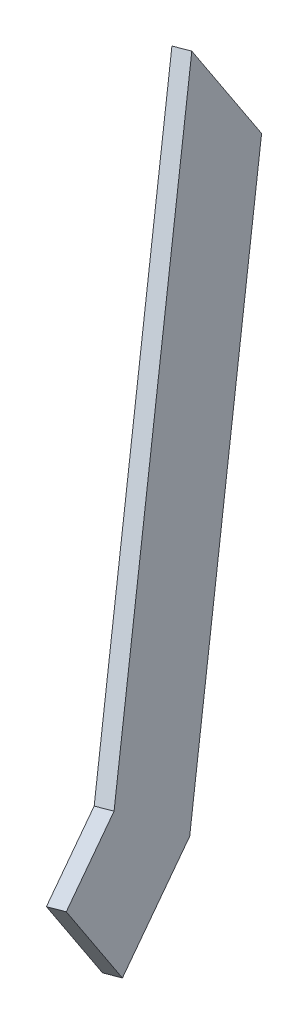
SolidWorks part; units mm, degrees
ref_plane "Front Plane" through (0, 0, 0) normal (0, 0, 1) x (1, 0, 0)
ref_plane "Top Plane" through (0, 0, 0) normal (0, 1, 0) x (1, 0, 0)
ref_plane "Right Plane" through (0, 0, 0) normal (1, 0, 0) x (0, 0, -1)
ref_plane "Plane1" through (-10.2412, -1.3482, 2.0513) normal (-0.9725, -0.128, 0.1948) x (-0.2331, 0.5341, -0.8126)
sketch "Sketch1" plane through (-10.2412, -1.3482, 2.0513) normal (-0.9725, -0.128, 0.1948) x (-0.2331, 0.5341, -0.8126)
  line L11 (240.1696, 267.4757) -> (-651.1692, 267.4757) construction
  line L16 (-309.3605, 268.4757) -> (-440.665, 365.4757)
  line L18 (-309.3605, 305.774) -> (-430.7857, 395.4757)
  line L19 (-430.7857, 395.4757) -> (-464.8592, 395.4757)
  line L20 (-440.665, 365.4757) -> (-464.8592, 365.4757)
  line L21 (-464.8592, 395.4757) -> (-464.8592, 365.4757)
  line L23 (-476.7605, 279.6757) -> (-309.3605, 279.6757) construction
  line L25 (-309.3605, 305.774) -> (-309.3605, 268.4757)
  line L26 (-309.3605, 284.6757) -> (-309.3605, 279.6757) construction
  line L28 (-476.7605, 365.4757) -> (-440.665, 365.4757) construction
  line L31 (-309.3605, 305.774) -> (-309.3605, -538.2869) construction
  arc A1 (-407.9685, 305.8635) -> (-445.5605, 305.8635) centre (-426.7645, 305.4757) ccw construction
  point P12 (-483.5268, 365.4757)
  point P29 (-309.3605, 267.4757)
  dimension "D2" = 40
  dimension "D1" = 1
  dimension "D4" = 30
  dimension "D7" = 30
extrude "Boss-Extrude1" add sketch "Sketch1" against normal blind 5
